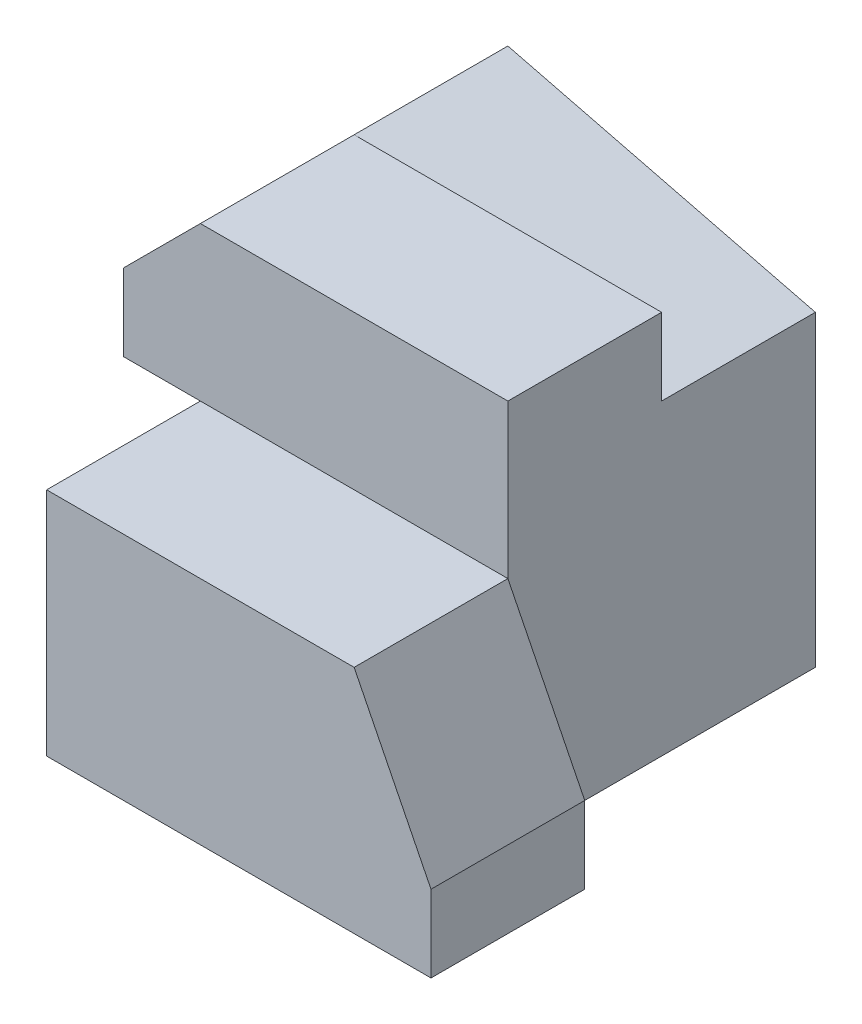
SolidWorks part; units mm, degrees
ref_plane "Front Plane" through (0, 0, 0) normal (0, 0, 1) x (1, 0, 0)
ref_plane "Top Plane" through (0, 0, 0) normal (0, 1, 0) x (1, 0, 0)
ref_plane "Right Plane" through (0, 0, 0) normal (1, 0, 0) x (0, 0, -1)
sketch "Sketch1" plane through (0, 0, 0) normal (0, 0, 1) x (1, 0, 0)
  line L0 (-25, 0) -> (-25, 15)
  line L1 (-25, 15) -> (-5, 15)
  line L2 (-5, 15) -> (0, 5)
  line L3 (0, 5) -> (0, 0)
  line L4 (0, 0) -> (-25, 0)
  dimension "D1" = 20
  dimension "D2" = 25
  dimension "D3" = 5
  dimension "D4" = 15
extrude "Boss-Extrude4" add sketch "Sketch1" along normal blind 10
sketch "Sketch3" plane through (0, 0, 0) normal (0, 0, -1) x (-1, 0, 0)
  line L0 (5, 15) -> (5, 0)
  line L1 (25, 0) -> (0, 0) construction
  line L2 (5, 0) -> (30, 0)
  line L3 (30, 0) -> (30, 5)
  line L4 (30, 5) -> (25, 15)
  line L5 (25, 15) -> (5, 15)
  dimension "D1" = 25
  dimension "D2" = 5
extrude "Boss-Extrude5" add sketch "Sketch3" along normal blind 10
sketch "Sketch4" plane through (0, 0, -10) normal (0, 0, -1) x (-1, 0, 0)
  line L2 (5, 15) -> (5, 25)
  line L3 (5, 25) -> (25, 25)
  line L4 (25, 25) -> (30, 20)
  line L5 (30, 20) -> (30, 15)
  line L7 (25, 15) -> (5, 15)
  line L8 (5, 15) -> (5, 0)
  line L9 (5, 0) -> (30, 0)
  line L10 (30, 0) -> (30, 5)
  line L11 (30, 5) -> (25, 15)
  line L12 (30, 15) -> (5, 15)
  dimension "D1" = 10
  dimension "D3" = 5
  dimension "D4" = 20
  dimension "D5" = 25
  dimension "D2" = 0
extrude "Boss-Extrude13" add sketch "Sketch4" against normal blind 10
sketch "Sketch9" plane through (0, 0, -10) normal (0, 0, -1) x (-1, 0, 0)
  line L1 (5, 0) -> (30, 0)
  line L2 (5, 0) -> (5, 20)
  line L3 (5, 20) -> (30, 20)
  line L4 (30, 0) -> (30, 20)
extrude "Boss-Extrude14" add sketch "Sketch9" along normal blind 10
sketch "Sketch10" plane through (0, 0, -10) normal (0, 0, -1) x (-1, 0, 0)
  line L0 (5, 20) -> (25, 25)
  line L1 (25, 25) -> (25, 20)
  line L2 (30, 20) -> (5, 20) construction
  line L3 (25, 20) -> (5, 20)
extrude "Boss-Extrude15" add sketch "Sketch10" along normal blind 10
